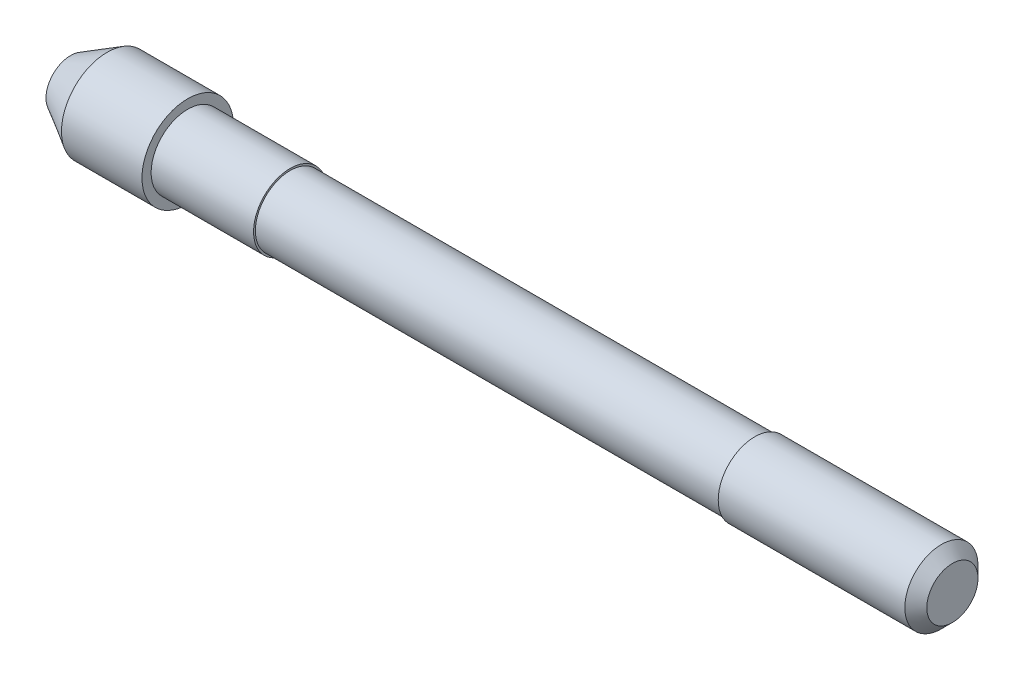
SolidWorks part; units mm, degrees
material "1.4301 (X5CrNi18-10)"
ref_plane "Face" through (0, 0, 0) normal (0, 0, 1) x (1, 0, 0)
ref_plane "Dessus" through (0, 0, 0) normal (0, 1, 0) x (1, 0, 0)
ref_plane "Droite" through (0, 0, 0) normal (1, 0, 0) x (0, 0, -1)
sketch "Esquisse1" plane through (0, 0, 0) normal (0, 0, 1) x (1, 0, 0)
  line L0 (-12.05, 0) -> (12.05, 0) construction
  line L1 (12.05, 0) -> (12.05, 1)
  line L2 (12.05, 1) -> (6.65, 1)
  line L3 (6.65, 1) -> (6.65, 0.95)
  line L4 (6.65, 0.95) -> (-6.05, 0.95)
  line L5 (-6.05, 0.95) -> (-6.05, 1)
  line L6 (-6.05, 1) -> (-8.85, 1)
  line L7 (-8.85, 1) -> (-8.85, 1.25)
  line L8 (-8.85, 1.25) -> (-11.05, 1.25)
  line L9 (-11.05, 1.25) -> (-12.05, 0.6726)
  line L10 (-12.05, 0.6726) -> (-12.05, 0)
  line L11 (-12.05, 0) -> (12.05, 0)
  dimension "D1" = 2
  dimension "D2" = 1.9
  dimension "D3" = 2
  dimension "D4" = 2.5
  dimension "D5" = 30
  dimension "D6" = 5.4
  dimension "D7" = 2.8
  dimension "D8" = 20.9
  dimension "D9" = 2.2
  dimension "D10" = 1
revolve "Révolution1" add sketch "Esquisse1" angle 360 about L0
chamfer "Chanfrein1" distance 0.3 angle 45 1 edges at (12.05, 0, 1)
